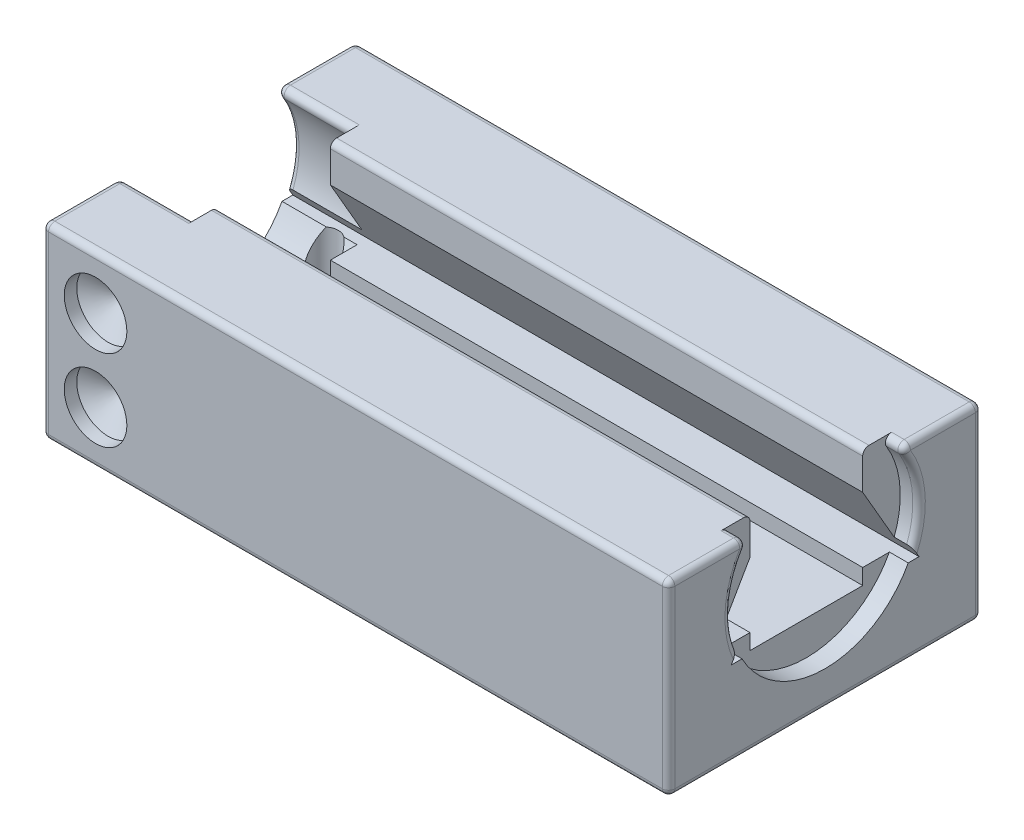
SolidWorks part; units mm, degrees
material "Polyetheretherketone (PEEK)"
ref_plane "Front Plane" through (0, 0, 0) normal (0, 0, 1) x (1, 0, 0)
ref_plane "Top Plane" through (0, 0, 0) normal (0, 1, 0) x (1, 0, 0)
ref_plane "Right Plane" through (0, 0, 0) normal (1, 0, 0) x (0, 0, -1)
ref_plane "Plane1" through (0, 4, 0) normal (0, 1, 0) x (-1, 0, 0)
sketch "Sketch1" plane through (0, 4, 0) normal (0, 1, 0) x (-1, 0, 0)
  line L0 (0, 0) -> (0, 5)
  line L1 (0, 5) -> (-10, 5)
  line L2 (-10, 5) -> (-10, 0)
  line L3 (-10, 0) -> (0, 0)
  dimension "D1" = 5
  dimension "D2" = 10
extrude "Boss-Extrude1" add sketch "Sketch1" against normal blind 3
sketch "Sketch18" plane through (10, 0, 0) normal (1, 0, 0) x (0, 0, -1)
  line L0 (-3.4, 3.4) -> (-4, 2.3608)
  line L1 (-5, 1) -> (-5, 4) construction
  line L2 (-4, 2.3608) -> (-3.4, 2.3608)
  line L3 (-3.4, 2.3608) -> (-3.4, 2.1108)
  line L4 (-1, 2.3608) -> (-1.6, 3.4)
  line L5 (-5, 4) -> (0, 4) construction
  line L6 (-3.4, 3.4) -> (-3.4, 4)
  line L7 (-3.4, 4) -> (-1.6, 4)
  line L8 (-3.4, 2.1108) -> (-1.6, 2.1108)
  line L9 (-1.6, 4) -> (-1.6, 3.4)
  line L10 (-1.6, 2.1108) -> (-1.6, 2.3608)
  line L11 (-1.6, 2.3608) -> (-1, 2.3608)
  dimension "D1" = 60
  dimension "D2" = 1.6
  dimension "D3" = 0.25
  dimension "D4" = 1.8
  dimension "D5" = 0.6
  dimension "D6" = 3
  dimension "D7" = 1.0392
extrude "Cut-Extrude9" cut sketch "Sketch18" against normal through all
sketch "Sketch20" plane through (0, 0, 0) normal (-1, 0, 0) x (0, 0, 1)
  line L0 (1.6, 2.3608) -> (1, 2.3608) construction
  circle A1 centre (2.5, 3.0608) radius 1.5
  dimension "D1" = 0.7
extrude "Cut-Extrude11" cut sketch "Sketch20" against normal blind 1.2
sketch "Sketch22" plane through (10, 0, 0) normal (1, 0, 0) x (0, 0, -1)
  circle A0 centre (-2.5, 3.0608) radius 1.5
  arc A1 (-3.8266, 2.3608) -> (-1.1734, 2.3608) centre (-2.5, 3.0608) ccw construction
  circle A2 centre (-2.5, 3.0608) radius 0.55
extrude "Cut-Extrude12" cut sketch "Sketch22" against normal blind 0.3
fillet "Fillet1" radius 0.1 10 edges at (9.85, 4, 1.3305) (9.85, 4, 3.6695) (5.45, 4, 3.4) (0.6, 4, 1.3305) (0.6, 4, 3.6695) (5.45, 4, 1.6) (5, 1, 5) (5, 1, 0) (5, 4, 0) (5, 4, 5)
fillet "Fillet2" radius 0.1 26 edges at (10, 3.203, 3.9932) (10, 3.9488, 3.7749) (10, 4, 4.3811) (10, 3.9707, 4.9707) (10, 1.0293, 4.9707) (10, 1.0293, 0.0293) (10, 3.203, 1.0068) (10, 3.9488, 1.2251) (10, 4, 0.6189) (10, 3.9707, 0.0293) (0, 3.203, 1.0068) (0, 3.9488, 1.2251) (0, 4, 0.6189) (0, 3.9707, 0.0293) (0, 1.0293, 0.0293) (0, 3.203, 3.9932) (0, 3.9488, 3.7749) (0, 4, 4.3811) (0, 3.9707, 4.9707) (0, 1.0293, 4.9707) (10, 2.5, 5) (10, 1, 2.5) (10, 2.5, 0) (0, 2.5, 0) (0, 2.5, 5) (0, 1, 2.5)
hole_wizard "Ø1.0mm Dowel Hole1" positions "Sketch25" profile "Sketch26" hole size "Ø1.0" standard "ANSI Metric"
sketch "Sketch25" plane through (0, 0, 5) normal (0, 0, 1) x (1, 0, 0)
  line L0 (9.9, 3.9) -> (0.1, 3.9) construction
  line L2 (0.1, 3.9) -> (0.1, 1.1) construction
  line L4 (0.1, 1.1) -> (9.9, 1.1) construction
  point P0 (0.85, 3.15)
  point P2 (0.85, 1.85)
  dimension "D1" = 0.75
  dimension "D2" = 0.75
  dimension "D3" = 0.75
  dimension "D4" = 0.75
sketch "Sketch26" plane through (0.85, 3.15, 5) normal (1, 0, 0) x (0, -1, 0)
  line L0 (0, 0) -> (0, 0.5004)
  line L1 (0, 0.5004) -> (0.5, 0.2)
  line L2 (0.5, 0.2) -> (0.5, 0)
  line L5 (0.5, 0) -> (0, 0)
  line L10 (0, 0.5004) -> (-0.5, 0.2) construction
  line L11 (0, -6.35) -> (0, 107.95) construction
  dimension "Hole Dia." = 1
  dimension "Hole Depth" = 0.2
  dimension "Drill Angle" = 118
hole_wizard "UNM0.6 Tapped Hole1" positions "Sketch27" profile "Sketch28" tap size "UNM0.6" standard "ANSI Metric"
sketch "Sketch27" plane through (0, 1, 0) normal (0, -1, 0) x (-1, 0, 0)
  line L0 (-9.9, -4.9) -> (-0.1, -4.9) construction
  line L1 (-0.1, -4.9) -> (-0.1, -0.1) construction
  point P0 (-0.85, -3.65)
  dimension "D1" = 1.25
  dimension "D2" = 0.75
sketch "Sketch28" plane through (0.85, 1, 3.65) normal (1, 0, 0) x (0, 0, -1)
  line L0 (0, 0) -> (0, 2.0852)
  line L1 (0, 2.0852) -> (0.225, 1.95)
  line L2 (0.225, 1.95) -> (0.225, 0)
  line L5 (0.225, 0) -> (0, 0)
  line L10 (0, 2.0852) -> (-0.225, 1.95) construction
  line L11 (0, -6.35) -> (0, 107.95) construction
  dimension "Tap Drill Dia." = 0.45
  dimension "Tap Drill Depth" = 1.95
  dimension "Drill Angle" = 118
ref_plane "midplane" through (0, 0, 2.5) normal (0, 0, -1) x (-1, 0, 0)
mirror "Mirror1" about plane through (0, 0, 2.5) normal (0, 0, -1) of "Ø1.0mm Dowel Hole1", "UNM0.6 Tapped Hole1"
